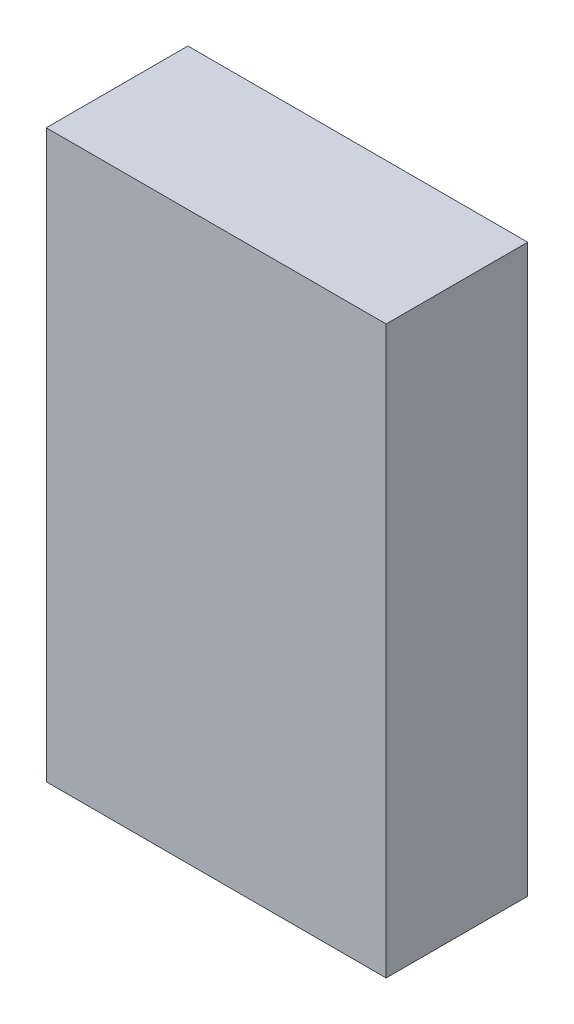
SolidWorks part; units mm, degrees
ref_plane "Front Plane" through (0, 0, 0) normal (0, 0, 1) x (1, 0, 0)
ref_plane "Top Plane" through (0, 0, 0) normal (0, 1, 0) x (1, 0, 0)
ref_plane "Right Plane" through (0, 0, 0) normal (1, 0, 0) x (0, 0, -1)
sketch "Sketch2" plane through (0, 0, 0) normal (0, 0, 1) x (1, 0, 0)
  line L1 (-8.5368, 6.0294) -> (-2.5368, 6.0294)
  line L2 (-8.5368, 6.0294) -> (-8.5368, -3.9706)
  line L3 (-8.5368, -3.9706) -> (-2.5368, -3.9706)
  line L4 (-2.5368, 6.0294) -> (-2.5368, -3.9706)
  dimension "D1" = 6
  dimension "D2" = 10
extrude "Boss-Extrude3" add sketch "Sketch2" along normal blind 2.5
